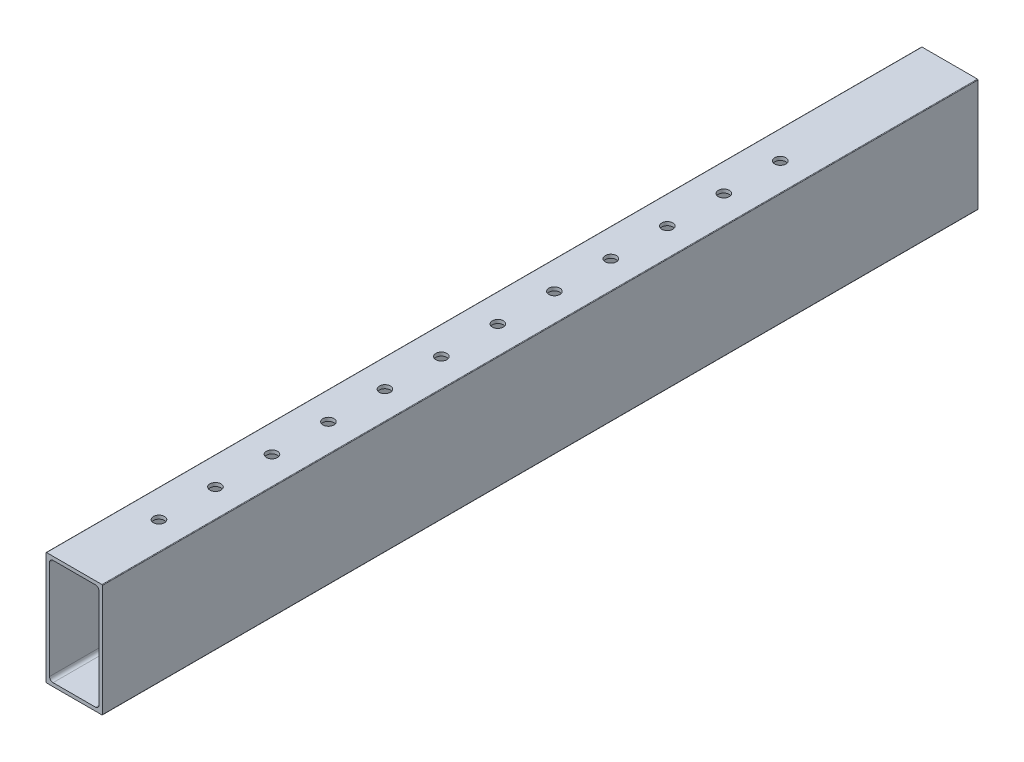
SolidWorks part; units mm, degrees
material "6061 Alloy"
ref_plane "Front Plane" through (0, 0, 0) normal (0, 0, 1) x (1, 0, 0)
ref_plane "Top Plane" through (0, 0, 0) normal (0, 1, 0) x (1, 0, 0)
ref_plane "Right Plane" through (0, 0, 0) normal (1, 0, 0) x (0, 0, -1)
ref_plane "Plane1" through (0, 0, 0) normal (0, 0, -1) x (-1, 0, 0)
sketch "Sketch1" plane through (0, 0, 0) normal (0, 0, -1) x (-1, 0, 0)
  line L0 (-11.1125, -22.225) -> (-11.1125, 22.225)
  line L1 (-9.525, 23.8125) -> (9.525, 23.8125)
  line L2 (11.1125, 22.225) -> (11.1125, -22.225)
  line L3 (9.525, -23.8125) -> (-9.525, -23.8125)
  line L4 (-12.7, 25.146) -> (-12.7, -25.146)
  line L5 (-12.446, -25.4) -> (12.446, -25.4)
  line L6 (12.7, -25.146) -> (12.7, 25.146)
  line L7 (12.446, 25.4) -> (-12.446, 25.4)
  arc A0 (-11.1125, 22.225) -> (-9.525, 23.8125) centre (-9.525, 22.225) cw
  arc A1 (9.525, 23.8125) -> (11.1125, 22.225) centre (9.525, 22.225) cw
  arc A2 (11.1125, -22.225) -> (9.525, -23.8125) centre (9.525, -22.225) cw
  arc A3 (-9.525, -23.8125) -> (-11.1125, -22.225) centre (-9.525, -22.225) cw
  arc A4 (-12.7, -25.146) -> (-12.446, -25.4) centre (-12.446, -25.146) ccw
  arc A5 (12.446, -25.4) -> (12.7, -25.146) centre (12.446, -25.146) ccw
  arc A6 (12.7, 25.146) -> (12.446, 25.4) centre (12.446, 25.146) ccw
  arc A7 (-12.446, 25.4) -> (-12.7, 25.146) centre (-12.446, 25.146) ccw
extrude "Boss-Extrude1" add sketch "Sketch1" against normal blind 393.7 from offset 88.9 offset against normal yes
sketch "Sketch3" plane through (0, -25.4, 0) normal (0, -1, 0) x (1, 0, 0)
  line L0 (0, 0) -> (0, 482.6) construction
  line L1 (12.446, 482.6) -> (-12.446, 482.6) construction
  line L2 (12.446, 88.9) -> (-12.446, 88.9) construction
  line L3 (-12.7, 355.6) -> (12.7, 355.6) construction
  line L4 (-12.7, 482.6) -> (-12.7, 88.9) construction
  line L5 (12.7, 482.6) -> (12.7, 88.9) construction
  circle A0 centre (0, 165.1) radius 2.4892
  circle A1 centre (0, 190.5) radius 2.4892
  circle A2 centre (0, 215.9) radius 2.4892
  circle A3 centre (0, 241.3) radius 2.4892
  circle A4 centre (0, 266.7) radius 2.4892
  circle A5 centre (0, 292.1) radius 2.4892
  circle A6 centre (0, 317.5) radius 2.4892
  circle A7 centre (0, 342.9) radius 2.4892
  circle A8 centre (0, 368.3) radius 2.4892
  circle A9 centre (0, 393.7) radius 2.4892
  circle A10 centre (0, 419.1) radius 2.4892
  circle A11 centre (0, 393.7) radius 2.4892
  circle A12 centre (0, 419.1) radius 2.4892
  circle A13 centre (0, 444.5) radius 2.4892
  dimension "D1" = 76.2
  dimension "D2" = 4.9784
  dimension "D3" = 12
  dimension "D4" = 25.4
  dimension "D5" = 38.1
extrude "Cut-Extrude2" cut sketch "Sketch3" against normal through all contours A8 | A9 | A13 | A10 | A7 | A6 | A5 | A4 | A3 | A2 | A1 | A0
